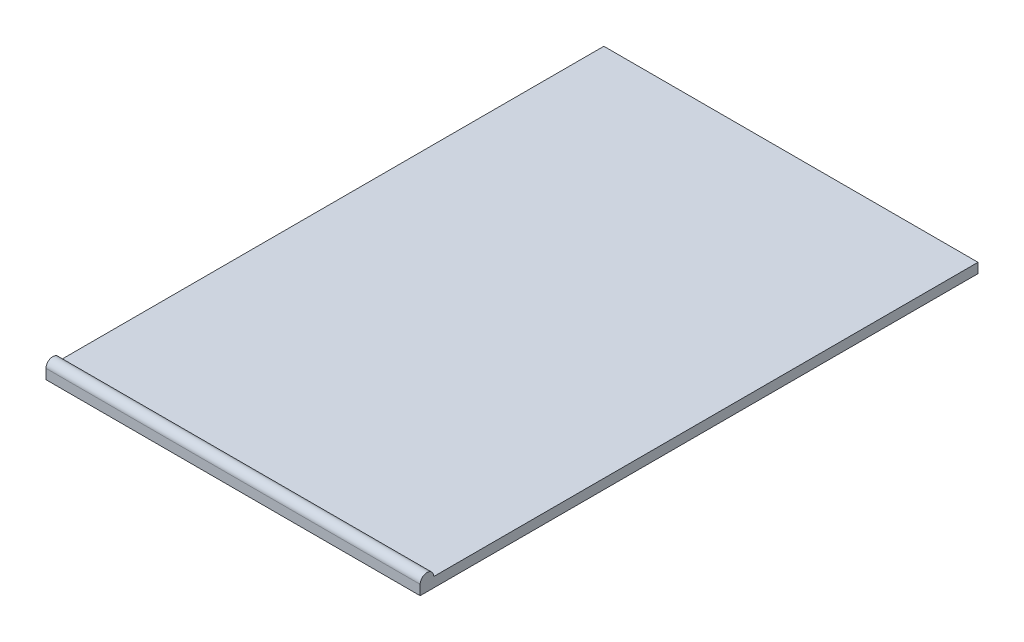
SolidWorks part; units mm, degrees
ref_plane "Front Plane" through (0, 0, 0) normal (0, 0, 1) x (1, 0, 0)
ref_plane "Top Plane" through (0, 0, 0) normal (0, 1, 0) x (1, 0, 0)
ref_plane "Right Plane" through (0, 0, 0) normal (1, 0, 0) x (0, 0, -1)
sketch "Sketch1" plane through (0, 0, 0) normal (0, 1, 0) x (1, 0, 0)
  line L0 (0, 0) -> (0, -164)
  line L1 (0, -164) -> (110, -164)
  line L2 (110, -164) -> (110, 0)
  line L3 (110, 0) -> (0, 0)
extrude "Boss-Extrude1" add sketch "Sketch1" along normal blind 2.9
sketch "Sketch2" plane through (0, 2.9, 0) normal (0, 1, 0) x (1, 0, 0)
  line L0 (0, -164) -> (110, -164)
  line L1 (110, -164) -> (110, -162)
  line L2 (110, -164) -> (110, 0) construction
  line L3 (110, -162) -> (0, -162)
  line L4 (0, 0) -> (0, -164) construction
  line L5 (0, -162) -> (0, -164)
revolve "Revolve1" add sketch "Sketch2" angle 180 about L3
